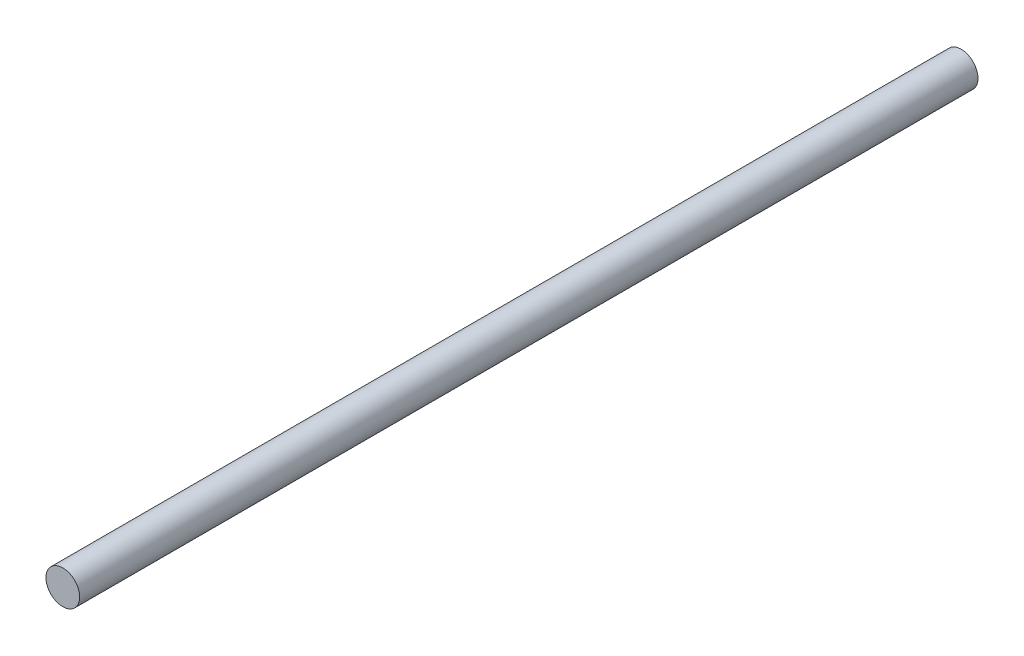
SolidWorks part; units mm, degrees
ref_plane "Ebene vorne" through (0, 0, 0) normal (0, 0, 1) x (1, 0, 0)
ref_plane "Ebene oben" through (0, 0, 0) normal (0, 1, 0) x (1, 0, 0)
ref_plane "Ebene rechts" through (0, 0, 0) normal (1, 0, 0) x (0, 0, -1)
sketch "Skizze1" plane through (0, 0, 0) normal (0, 0, 1) x (1, 0, 0)
  circle A0 centre (0, 0) radius 1.5
  dimension "D1" = 3
extrude "Aufsatz-Linear austragen1" add sketch "Skizze1" along normal blind 80
